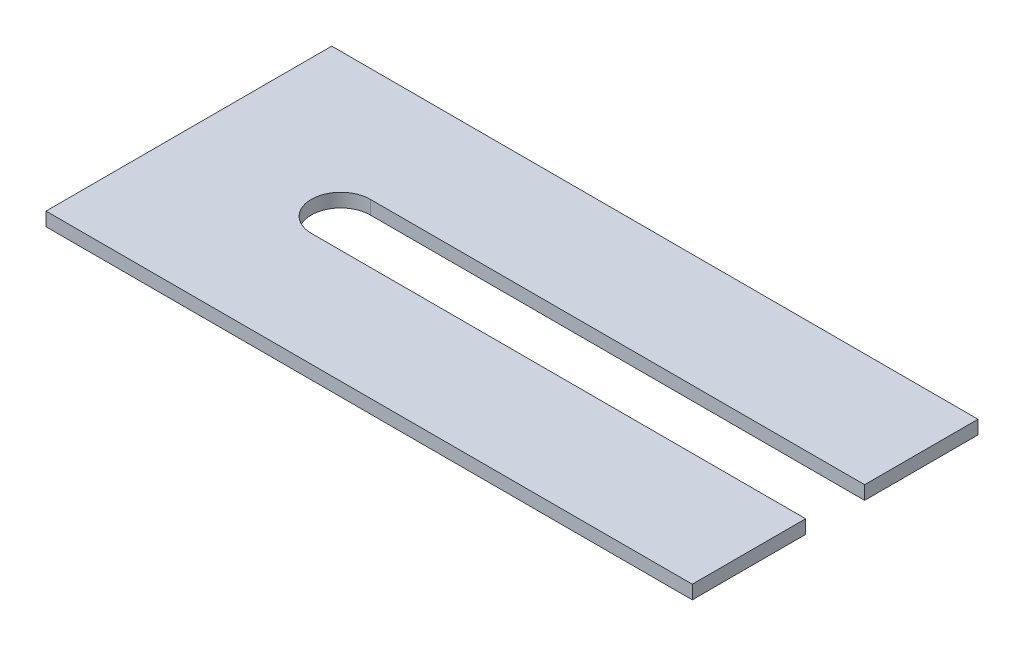
SolidWorks part; units mm, degrees
ref_plane "Front Plane" through (0, 0, 0) normal (0, 0, 1) x (1, 0, 0)
ref_plane "Top Plane" through (0, 0, 0) normal (0, 1, 0) x (1, 0, 0)
ref_plane "Right Plane" through (0, 0, 0) normal (1, 0, 0) x (0, 0, -1)
sketch "Sketch1" plane through (0, 0, 0) normal (0, 1, 0) x (1, 0, 0)
  line L0 (71.25, 15.75) -> (16.75, 15.75) construction
  line L1 (0, 0) -> (71.25, 0)
  line L2 (0, 0) -> (0, 31.5)
  line L3 (0, 31.5) -> (71.25, 31.5)
  line L4 (71.25, 0) -> (71.25, 31.5)
  line L5 (0, 0) -> (71.25, 31.5) construction
  line L6 (0, 31.5) -> (71.25, 0) construction
  line L7 (71.25, 12.5) -> (16.75, 12.5)
  line L8 (71.25, 19) -> (16.75, 19)
  line L9 (71.25, 19) -> (71.25, 12.5)
  arc A0 (71.25, 12.5) -> (71.25, 19) centre (71.25, 15.75) ccw
  arc A1 (16.75, 19) -> (16.75, 12.5) centre (16.75, 15.75) ccw
  point P4 (35.625, 15.75)
  point P8 (44, 15.75)
  point P13 (13.5, 15.75)
  dimension "D1" = 31.5
  dimension "D2" = 71.25
  dimension "D3" = 6.5
  dimension "D4" = 13.5
extrude "Boss-Extrude1" add sketch "Sketch1" along normal blind 1.5 contours A1 L8 L4 L3 L2 L1 L7
